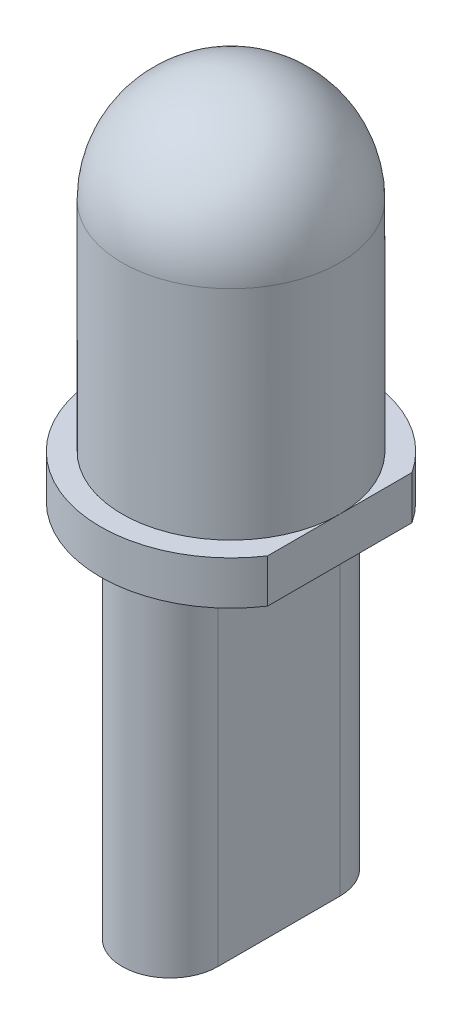
SolidWorks part; units mm, degrees
ref_plane "Front Plane" through (0, 0, 0) normal (0, 0, 1) x (1, 0, 0)
ref_plane "Top Plane" through (0, 0, 0) normal (0, 1, 0) x (1, 0, 0)
ref_plane "Right Plane" through (0, 0, 0) normal (1, 0, 0) x (0, 0, -1)
sketch "Sketch1" plane through (0, 0, 0) normal (0, 0, 1) x (1, 0, 0)
  line L0 (0, 0) -> (0, 8.5)
  line L1 (0, 0) -> (3, 0)
  line L2 (3, 0) -> (3, 1)
  line L3 (3, 1) -> (2.5, 1)
  line L4 (2.5, 1) -> (2.5, 6)
  arc A0 (0, 8.5) -> (2.5, 6) centre (0, 6) cw
  dimension "D1" = 2.5
  dimension "D2" = 3
  dimension "D3" = 1
  dimension "D4" = 8.5
revolve "Revolve1" add sketch "Sketch1" angle 360 about L0
sketch "Sketch2" plane through (0, 1, 0) normal (0, 1, 0) x (1, 0, 0)
  line L0 (2.5, 1.6583) -> (2.5, -1.6583)
  circle A0 centre (0, 0) radius 3 construction
  arc A1 (2.5, -1.6583) -> (2.5, 1.6583) centre (0, 0) ccw
  circle A2 centre (0, 0) radius 2.5 construction
extrude "Cut-Extrude1" cut sketch "Sketch2" against normal up to next
sketch "Sketch3" plane through (0, 0, 0) normal (0, -1, 0) x (1, 0, 0)
  line L0 (0, 1.4) -> (0, -1.4) construction
  line L1 (1.1, 1.4) -> (1.1, -1.4)
  line L2 (-1.1, 1.4) -> (-1.1, -1.4)
  arc A0 (1.1, 1.4) -> (-1.1, 1.4) centre (0, 1.4) ccw
  arc A1 (-1.1, -1.4) -> (1.1, -1.4) centre (0, -1.4) ccw
  point P2 (0, 0)
  dimension "D2" = 5
  dimension "D1" = 2.2
extrude "Boss-Extrude1" add sketch "Sketch3" along normal blind 8
